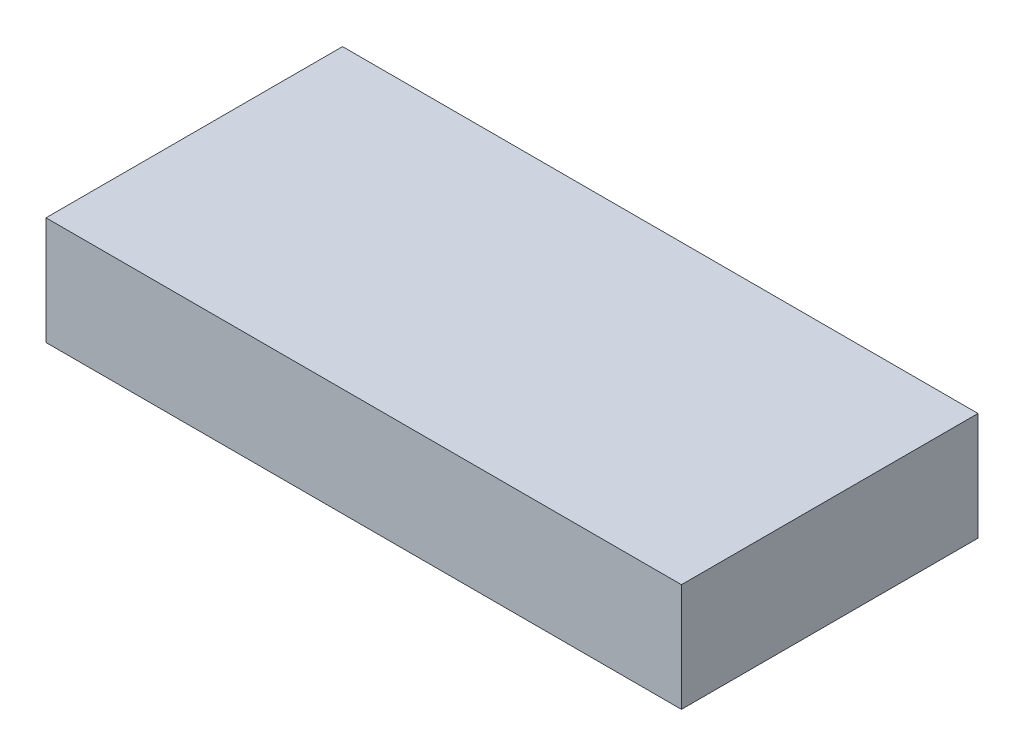
SolidWorks part; units mm, degrees
ref_plane "前视基准面" through (0, 0, 0) normal (0, 0, 1) x (1, 0, 0)
ref_plane "上视基准面" through (0, 0, 0) normal (0, 1, 0) x (1, 0, 0)
ref_plane "右视基准面" through (0, 0, 0) normal (1, 0, 0) x (0, 0, -1)
other "Configuration Table"
sketch "草图2" plane through (0, 0, 0) normal (0, 1, 0) x (1, 0, 0)
  line L1 (-19.7193, 9.193) -> (40.2807, 9.193)
  line L2 (-19.7193, 9.193) -> (-19.7193, -18.807)
  line L3 (-19.7193, -18.807) -> (40.2807, -18.807)
  line L4 (40.2807, 9.193) -> (40.2807, -18.807)
  dimension "D1" = 60
  dimension "D2" = 28
extrude "凸台-拉伸1" add sketch "草图2" along normal blind 10.2
sketch "草图3" plane through (0, 0, 0) normal (0, -1, 0) x (1, 0, 0)
  line L0 (-21.8822, 4.807) -> (-8.6441, 4.807) construction
  line L2 (40.2807, 18.807) -> (40.2807, -9.193) construction
  circle A0 centre (21.2807, 4.807) radius 7
  dimension "D1" = 14
  dimension "D2" = 19
extrude "凸台-拉伸2" add sketch "草图3" along normal blind 2.4
